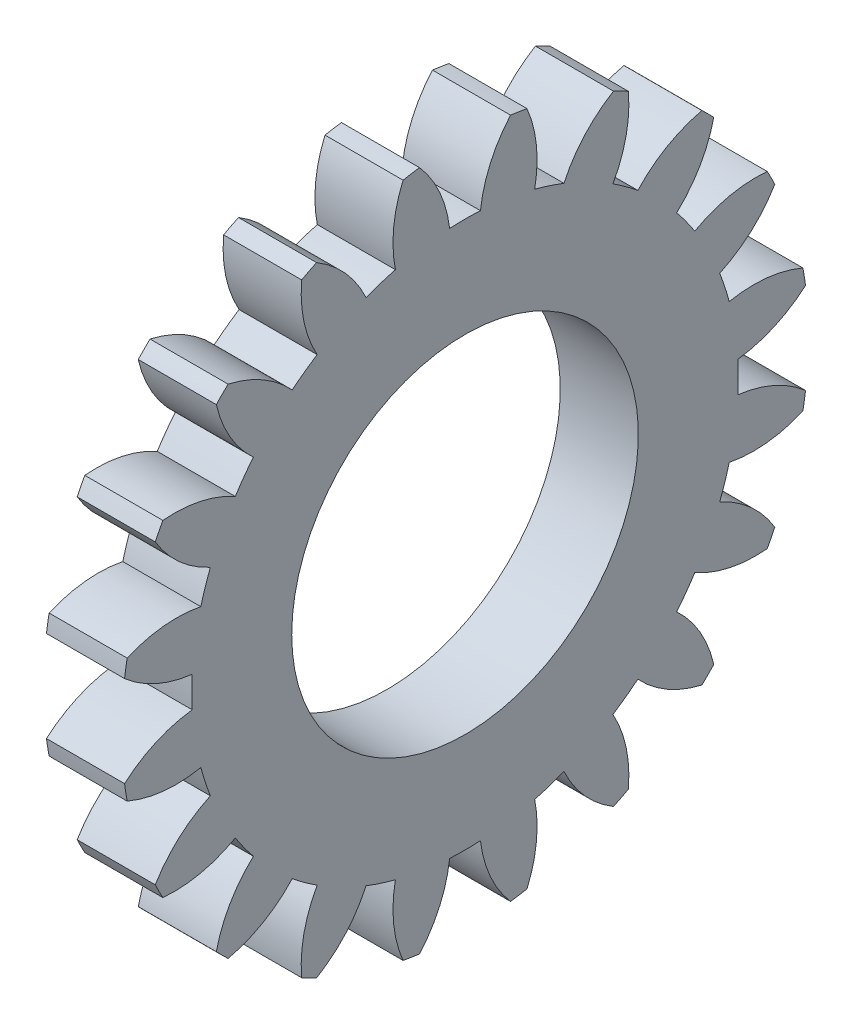
SolidWorks part; units mm, degrees
ref_plane "Plane1" through (0, 0, 0) normal (0, 0, 1) x (1, 0, 0)
ref_plane "Plane2" through (0, 0, 0) normal (0, 1, 0) x (1, 0, 0)
ref_plane "Plane3" through (0, 0, 0) normal (1, 0, 0) x (0, 0, -1)
other "Configuration Table"
sketch "HoldingSke" plane through (0, 0, 0) normal (0, 1, 0) x (1, 0, 0)
  line L0 (0, 0) -> (0.4698, -0.171)
  line L1 (-15, 0) -> (100, 0) construction
  line L2 (0, 0) -> (-2.1039, 2.3779)
  line L3 (0, 0) -> (-11.863, 4.5341)
  line L4 (0, 0) -> (8.1152, 2.9537)
  line L5 (0, 0) -> (-46.8476, -17.4728)
  line L6 (0, 0) -> (-4.1448, -2.7965)
  line L7 (-2.1039, 2.3779) -> (8.6586, 51.2059)
  line L8 (-76.2, 54.61) -> (-76.1, 54.61)
  line L9 (-71.009, 38.7566) -> (-53.1078, 45.2721)
  line L10 (-76.2, 71.12) -> (104.1128, 71.12)
  line L11 (0, 0) -> (-5, 0)
  line L12 (-76.2, 101.6) -> (-76.133, 101.6)
  line L13 (24.9733, 27.94) -> (52.9518, 28.4284)
  line L14 (24.9733, 27.94) -> (24.9743, 27.94)
  line L15 (24.9733, 27.94) -> (100.4006, 29.5858)
  line L16 (-63.627, -2) -> (-12.827, -2)
  circle A0 centre (0, 0) radius 0.5
  circle A1 centre (0, 0) radius 17.499
  circle A2 centre (0, 0) radius 37.5
  circle A3 centre (0, 0) radius 0.5
  dimension "MHD" = 34.998
  dimension "Hub_dia" = 75
  dimension "Bore" = 1
  dimension "MBD" = 1
  dimension "Num_teeth" = 20
  dimension "Pitch" = 0.5
  dimension "Overall_len" = 50
  dimension "Show_teeth" = 20
  dimension "Thickness" = 5
  dimension "OAL" = 50.0001
  dimension "T_dim" = 0.1
  dimension "Ap" = 20
  dimension "H" = 19.05
  dimension "Pitch_radius" = 180.3128
  dimension "Width" = 5
  dimension "Backlash" = 0.067
  dimension "Addendum_fac" = 1
  dimension "Dedendum_fac" = 1.25
  dimension "Clearance_fac" = 0.25
  dimension "Dedendum_add" = 0.001
  dimension "Module" = 2
sketch "BasProSke" plane through (0, 0, 0) normal (0, 1, 0) x (1, 0, 0)
  line L0 (-10, 0) -> (60, 0) construction
  line L1 (0, 0) -> (0, 22)
  line L2 (0, 0) -> (5, 0)
  line L3 (5, 0) -> (5, 22)
  line L4 (5, 22) -> (0, 22)
  dimension "Thickness" = 5
  dimension "Diameter" = 44
revolve "Base-Revolve" add sketch "BasProSke" angle 360 about L0
sketch "TooCutSke" plane through (0, 0, 0) normal (1, 0, 0) x (0, 0, -1)
  line L1 (0, 0) -> (0, 107) construction
  line L2 (0, 0) -> (-1.6864, 19.9288) construction
  line L3 (0, 0) -> (-6.2409, 39.4033) construction
  line L4 (-1.6864, 19.9288) -> (-3.1204, 19.7016) construction
  arc A0 (0.9862, 17.4712) -> (-0.9862, 17.4712) centre (0, 0) ccw
  arc A1 (2.9329, 21.8293) -> (-2.9329, 21.8293) centre (0, 0) ccw
  circle A2 centre (0, 0) radius 20 construction
  circle A3 centre (0, 0) radius 18.7939 construction
  arc A4 (-0.9862, 17.4712) -> (-2.9329, 21.8293) centre (-8.9313, 16.536) ccw
  arc A5 (2.9329, 21.8293) -> (0.9862, 17.4712) centre (8.9313, 16.536) ccw
  dimension "Root_dia" = 34.998
  dimension "Overcut_dia" = 44.0508
  dimension "Pitch_dia" = 40
  dimension "Base_dia" = 37.5877
  dimension "Flank_rad" = 8
  dimension "Half_ang" = 9
  dimension "Half_CT" = 1.4519
extrude "ToothCut" cut sketch "TooCutSke" along normal through all
fillet "Breaks" [suppressed] radius 0.04
fillet "RootFillets" [suppressed] radius 0.501
pattern_circular "TeethCuts" count 20 every 18 about axis through (-10, 0, 0) along (1, 0, 0) of "ToothCut", "RootFillets", "Breaks"
sketch "HubNeaOneSke" plane through (0, 0, 0) normal (-1, 0, 0) x (0, 0, 1)
  circle A0 centre (0, 0) radius 17.499
  dimension "Diameter" = 34.998
extrude "HubNearOne" [suppressed] add sketch "HubNeaOneSke" along normal blind 45.0001
sketch "HubNeaBotSke" plane through (0, 0, 0) normal (-1, 0, 0) x (0, 0, 1)
  circle A0 centre (0, 0) radius 17.499
  dimension "Diameter" = 34.998
extrude "HubNearBoth" [suppressed] add sketch "HubNeaBotSke" along normal blind 22.5
ref_plane "FarPln" through (5, 0, 0) normal (1, 0, 0) x (0, 0, -1)
sketch "HubFarSke" plane through (5, 0, 0) normal (1, 0, 0) x (0, 0, -1)
  circle A0 centre (0, 0) radius 17.499
  dimension "Diameter" = 34.998
extrude "HubFar" [suppressed] add sketch "HubFarSke" along normal blind 22.5
sketch "BorSke" plane through (0, 0, 0) normal (1, 0, 0) x (0, 0, -1)
  circle A0 centre (0, 0) radius 0.5
  dimension "Diameter" = 1
extrude "Bore" cut sketch "BorSke" along normal mid plane 100.0001
sketch "KeySke" plane through (0, 0, 0) normal (1, 0, 0) x (0, 0, -1)
  line L0 (-0.05, 0) -> (-0.05, 0.6)
  line L1 (-0.05, 0.6) -> (0.05, 0.6)
  line L2 (0.05, 0.6) -> (0.05, 0)
  line L3 (0, 0) -> (0, 34) construction
  line L4 (-0.05, 0) -> (0.05, 0)
  dimension "Offset" = 0.6
  dimension "Width" = 0.1
extrude "Keyway" [suppressed] cut sketch "KeySke" along normal mid plane 100.0001
pattern_circular "Keyway2" [suppressed] count 2 every 90 about axis through (-10, 0, 0) along (1, 0, 0)
sketch "Sketch1" plane through (0, 0, 0) normal (-1, 0, 0) x (0, 0, 1)
  circle A0 centre (0, 0) radius 11.1
extrude "Cut-Extrude1" cut sketch "Sketch1" against normal blind 10
equation "' \"Module@HoldingSke\" = 6.35"
equation "' \"Num_teeth@HoldingSke\" = 12"
equation "' \"Ap@HoldingSke\" =  20"
equation "' \"Ap@HoldingSke\" = 20"
equation "' \"Width@HoldingSke\" = 0.5 * 25.4"
equation "' \"Hub_dia@HoldingSke\"= 1 * 25.4"
equation "' \"Hub_dia@HoldingSke\" = 1 * 25.4"
equation "' \"Overall_len@HoldingSke\" = 1.0 * 25.4"
equation "' \"Bore@HoldingSke\" = 0.75 * 25.4"
equation "' \"T_dim@HoldingSke\" = 0.1 * 25.4"
equation "' \"Width@KeySke\" = 0.25 * 25.4"
equation "' \"Show_teeth@HoldingSke\" = 13"
equation "' \"Backlash@HoldingSke\" = 0.009 * 25.4"
equation "' \"Addendum_fac@HoldingSke\" = 1.0"
equation "' \"Dedendum_fac@HoldingSke\" = 1.25"
equation "' \"Dedendum_add@HoldingSke\" = 0.00005 * 25.4"
equation "' \"Clearance_fac@HoldingSke\" = 0.25"
equation "\"Pitch@HoldingSke\" = 1 / \"Module@HoldingSke\""
equation "\"Overcut_dia@TooCutSke\" = (\"Num_teeth@HoldingSke\" + 2 * \"Addendum_fac@HoldingSke\") / \"Pitch@HoldingSke\" + 0.002 * 25.4"
equation "\"Pitch_dia@TooCutSke\" = \"Num_teeth@HoldingSke\" / \"Pitch@HoldingSke\""
equation "\"Base_dia@TooCutSke\" = \"Num_teeth@HoldingSke\" / \"Pitch@HoldingSke\" * cos((\"Ap@HoldingSke\"  * 3.14159265 / 180))"
equation "\"Root_dia@TooCutSke\" = (\"Num_teeth@HoldingSke\" + 2) / \"Pitch@HoldingSke\" - 2 * (\"Addendum_fac@HoldingSke\" + \"Dedendum_fac@HoldingSke\") / \"Pitch@HoldingSke\" - \"Dedendum_add@HoldingSke\" * 2"
equation "\"Half_ang@TooCutSke\" = 180 / \"Num_teeth@HoldingSke\""
equation "\"Half_CT@TooCutSke\" = \"Num_teeth@HoldingSke\" / \"Pitch@HoldingSke\" * sin((3.14159265 / 2 / \"Num_teeth@HoldingSke\")) / 2 - 7 * \"Backlash@HoldingSke\" / 4"
equation "\"Flank_rad@TooCutSke\" = \"Num_teeth@HoldingSke\" / \"Pitch@HoldingSke\" / 5"
equation "\"Radius@RootFillets\" = \"Clearance_fac@HoldingSke\" / \"Pitch@HoldingSke\" + \"Dedendum_add@HoldingSke\""
equation "\"Break_rad@Breaks\" = 0.02 / \"Pitch@HoldingSke\""
equation "\"Thickness@HoldingSke\" = \"Width@HoldingSke\""
equation "\"OAL@HoldingSke\" = \"Thickness@HoldingSke\""
equation "\"MHD@HoldingSke\" = (\"Num_teeth@HoldingSke\" + 2) / \"Pitch@HoldingSke\" - 2 * (\"Addendum_fac@HoldingSke\" + \"Dedendum_fac@HoldingSke\")  / \"Pitch@HoldingSke\" - \"Dedendum_add@HoldingSke\" * 2"
equation "\"MBD@HoldingSke\" = (\"Num_teeth@HoldingSke\" + 2) / \"Pitch@HoldingSke\" - 2 * (\"Addendum_fac@HoldingSke\" + \"Dedendum_fac@HoldingSke\")  / \"Pitch@HoldingSke\" - \"Dedendum_add@HoldingSke\" * 2 - 0.002 * 25.4"
equation "\"MHD@HoldingSke\" = ((sgn( \"MHD@HoldingSke\" - \"Hub_dia@HoldingSke\" )-1)*( \"MHD@HoldingSke\" - \"Hub_dia@HoldingSke\" ))/-2+ \"Hub_dia@HoldingSke\""
equation "\"MBD@HoldingSke\" = ((sgn( \"MBD@HoldingSke\" - \"Bore@HoldingSke\" )-1)*( \"MBD@HoldingSke\" - \"Bore@HoldingSke\" ))/-2+ \"Bore@HoldingSke\""
equation "\"OAL@HoldingSke\" = ((sgn( \"OAL@HoldingSke\" - \"Overall_len@HoldingSke\" )+1)*( \"OAL@HoldingSke\" - \"Overall_len@HoldingSke\" ))/2 + \"Overall_len@HoldingSke\" + 0.000002 * 25.4"
equation "\"Num_teeth@TeethCuts\" = int( \"Show_teeth@HoldingSke\" ) + 1"
equation "\"Num_teeth@TeethCuts\" = ((sgn( \"Num_teeth@TeethCuts\" - \"Num_teeth@HoldingSke\" )-1)*( \"Num_teeth@TeethCuts\" - \"Num_teeth@HoldingSke\" ))/-2+ \"Num_teeth@HoldingSke\""
equation "\"Num_teeth@TeethCuts\" = ((sgn( \"Num_teeth@TeethCuts\" - 2.0)+1)*( \"Num_teeth@TeethCuts\" - 2.0))/2 +2.0"
equation "\"Angle@TeethCuts\" = 360.0 / \"Num_teeth@HoldingSke\""
equation "\"Diameter@BasProSke\" = (\"Num_teeth@HoldingSke\" + 2 * \"Addendum_fac@HoldingSke\") / \"Pitch@HoldingSke\""
equation "\"Thickness@BasProSke\"  = \"Thickness@HoldingSke\""
equation "' \"Fillet_rad@BasProSke\" =  \"Thickness@HoldingSke\" * 0.05"
equation "' \"Fillet_rad@BasProSke\" = \"Thickness@HoldingSke\" * 0.05"
equation "\"MHD@HoldingSke\" = ((sgn( \"MHD@HoldingSke\" - \"Root_dia@TooCutSke\" )-1)*( \"MHD@HoldingSke\" - \"Root_dia@TooCutSke\" ))/-2+ \"Root_dia@TooCutSke\""
equation "\"Diameter@HubNeaOneSke\" = \"MHD@HoldingSke\""
equation "\"Length@HubNearOne\" = \"OAL@HoldingSke\" - \"Thickness@BasProSke\""
equation "\"Diameter@HubNeaBotSke\" = \"MHD@HoldingSke\""
equation "\"Length@HubNearBoth\" = ( \"OAL@HoldingSke\" - \"Thickness@BasProSke\" ) / 2.0"
equation "\"Thickness@FarPln\" = \"Thickness@BasProSke\""
equation "\"Diameter@HubFarSke\" = \"MHD@HoldingSke\""
equation "\"Length@HubFar\" = ( \"OAL@HoldingSke\" - \"Thickness@BasProSke\" ) / 2.0"
equation "\"Diameter@BorSke\" = \"MBD@HoldingSke\""
equation "\"D1@Bore\" = \"OAL@HoldingSke\" * 2.0"
equation "\"D1@Keyway\" = \"OAL@HoldingSke\" * 2.0"
equation "\"Offset@KeySke\" = \"T_dim@HoldingSke\" + \"MBD@HoldingSke\" / 2.0"
